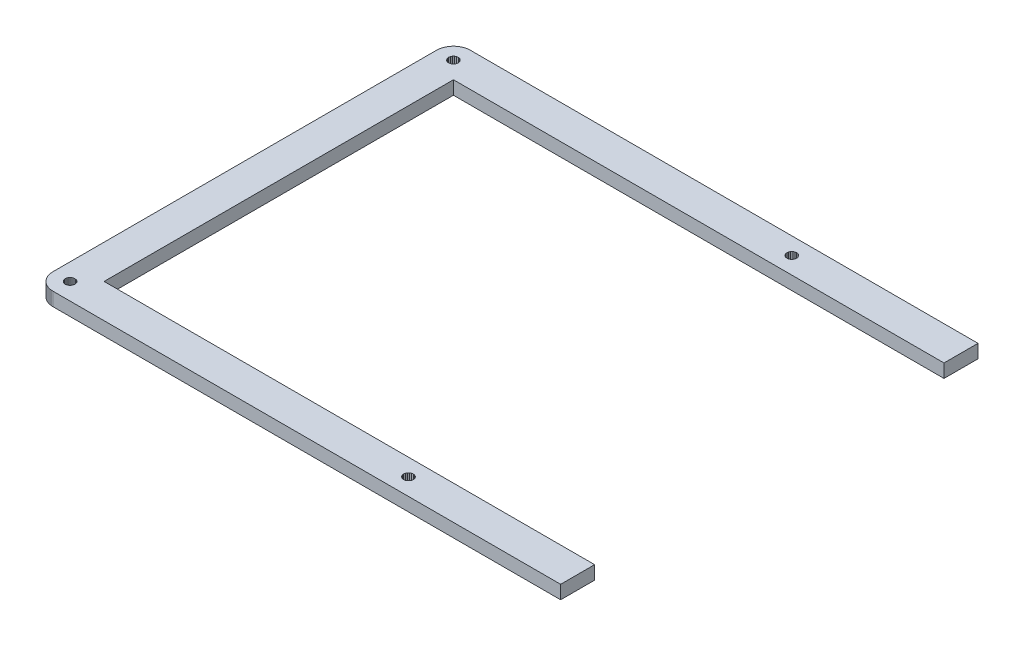
SolidWorks part; units mm, degrees
material "Copper"
ref_plane "Front Plane" through (0, 0, 0) normal (0, 0, 1) x (1, 0, 0)
ref_plane "Top Plane" through (0, 0, 0) normal (0, 1, 0) x (1, 0, 0)
ref_plane "Right Plane" through (0, 0, 0) normal (1, 0, 0) x (0, 0, -1)
sketch "Sketch1" plane through (0, 0, 0) normal (0, 1, 0) x (1, 0, 0)
  line L0 (365.806, 147.967) -> (366.279, 147.949)
  line L1 (366.279, 147.949) -> (366.748, 147.894)
  line L2 (366.748, 147.894) -> (367.21, 147.803)
  line L3 (367.21, 147.803) -> (367.661, 147.675)
  line L4 (367.661, 147.675) -> (368.106, 147.511)
  line L5 (368.106, 147.511) -> (368.533, 147.314)
  line L6 (368.533, 147.314) -> (368.942, 147.085)
  line L7 (368.942, 147.085) -> (369.334, 146.822)
  line L8 (369.334, 146.822) -> (369.704, 146.529)
  line L9 (369.704, 146.529) -> (370.05, 146.21)
  line L10 (370.05, 146.21) -> (370.371, 145.865)
  line L11 (370.371, 145.865) -> (370.664, 145.495)
  line L12 (370.664, 145.495) -> (370.925, 145.102)
  line L13 (370.925, 145.102) -> (371.154, 144.691)
  line L14 (371.154, 144.691) -> (371.352, 144.264)
  line L15 (371.352, 144.264) -> (371.514, 143.822)
  line L16 (371.514, 143.822) -> (371.641, 143.368)
  line L17 (371.641, 143.368) -> (371.733, 142.907)
  line L18 (371.733, 142.907) -> (371.789, 142.44)
  line L19 (371.789, 142.44) -> (371.807, 141.967)
  line L20 (371.807, 141.967) -> (371.807, 6.0909)
  line L21 (371.807, 6.0909) -> (371.789, 5.621)
  line L22 (371.789, 5.621) -> (371.733, 5.1539)
  line L23 (371.733, 5.1539) -> (371.641, 4.6909)
  line L24 (371.641, 4.6909) -> (371.514, 4.2375)
  line L25 (371.514, 4.2375) -> (371.352, 3.7951)
  line L26 (371.352, 3.7951) -> (371.154, 3.3679)
  line L27 (371.154, 3.3679) -> (370.925, 2.9573)
  line L28 (370.925, 2.9573) -> (370.664, 2.5645)
  line L29 (370.664, 2.5645) -> (370.371, 2.1966)
  line L30 (370.371, 2.1966) -> (370.05, 1.8493)
  line L31 (370.05, 1.8493) -> (369.704, 1.5296)
  line L32 (369.704, 1.5296) -> (369.334, 1.2375)
  line L33 (369.334, 1.2375) -> (368.942, 0.9757)
  line L34 (368.942, 0.9757) -> (368.533, 0.7455)
  line L35 (368.533, 0.7455) -> (368.106, 0.5498)
  line L36 (368.106, 0.5498) -> (367.661, 0.3859)
  line L37 (367.661, 0.3859) -> (367.21, 0.2577)
  line L38 (367.21, 0.2577) -> (366.748, 0.1654)
  line L39 (366.748, 0.1654) -> (366.279, 0.1102)
  line L40 (366.279, 0.1102) -> (365.806, 0.091)
  line L41 (365.806, 0.091) -> (6.095, 0.091)
  line L42 (6.095, 0.091) -> (5.6238, 0.1102)
  line L43 (5.6238, 0.1102) -> (5.1553, 0.1654)
  line L44 (5.1553, 0.1654) -> (4.6936, 0.2577)
  line L45 (4.6936, 0.2577) -> (4.2402, 0.3859)
  line L46 (4.2402, 0.3859) -> (3.7979, 0.5498)
  line L47 (3.7979, 0.5498) -> (3.3707, 0.7455)
  line L48 (3.3707, 0.7455) -> (2.96, 0.9757)
  line L49 (2.96, 0.9757) -> (2.5673, 1.2375)
  line L50 (2.5673, 1.2375) -> (2.198, 1.5296)
  line L51 (2.198, 1.5296) -> (1.8521, 1.8493)
  line L52 (1.8521, 1.8493) -> (1.5324, 2.1966)
  line L53 (1.5324, 2.1966) -> (1.2402, 2.5645)
  line L54 (1.2402, 2.5645) -> (0.9784, 2.9573)
  line L55 (0.9784, 2.9573) -> (0.7483, 3.3679)
  line L56 (0.7483, 3.3679) -> (0.5512, 3.7951)
  line L57 (0.5512, 3.7951) -> (0.3872, 4.2375)
  line L58 (0.3872, 4.2375) -> (0.2591, 4.6909)
  line L59 (0.2591, 4.6909) -> (0.1681, 5.1539)
  line L60 (0.1681, 5.1539) -> (0.113, 5.621)
  line L61 (0.113, 5.621) -> (0.0937, 6.0923)
  line L62 (0.0937, 6.0923) -> (0.0951, 141.967)
  line L63 (0.0951, 141.967) -> (0.113, 142.44)
  line L64 (0.113, 142.44) -> (0.1681, 142.907)
  line L65 (0.1681, 142.907) -> (0.2591, 143.368)
  line L66 (0.2591, 143.368) -> (0.3872, 143.822)
  line L67 (0.3872, 143.822) -> (0.5512, 144.264)
  line L68 (0.5512, 144.264) -> (0.7483, 144.691)
  line L69 (0.7483, 144.691) -> (0.9784, 145.102)
  line L70 (0.9784, 145.102) -> (1.2402, 145.495)
  line L71 (1.2402, 145.495) -> (1.5324, 145.865)
  line L72 (1.5324, 145.865) -> (1.8521, 146.21)
  line L73 (1.8521, 146.21) -> (2.198, 146.529)
  line L74 (2.198, 146.529) -> (2.5673, 146.822)
  line L75 (2.5673, 146.822) -> (2.96, 147.085)
  line L76 (2.96, 147.085) -> (3.3707, 147.314)
  line L77 (3.3707, 147.314) -> (3.7979, 147.511)
  line L78 (3.7979, 147.511) -> (4.2402, 147.675)
  line L79 (4.2402, 147.675) -> (4.6936, 147.803)
  line L80 (4.6936, 147.803) -> (5.1553, 147.894)
  line L81 (5.1553, 147.894) -> (5.6238, 147.949)
  line L82 (5.6238, 147.949) -> (6.095, 147.968)
  line L83 (6.095, 147.968) -> (365.806, 147.967)
  line L84 (365.252, 7.757) -> (364.769, 7.5117)
  line L85 (364.769, 7.5117) -> (364.388, 7.13)
  line L86 (364.388, 7.13) -> (364.141, 6.6504)
  line L87 (364.141, 6.6504) -> (364.06, 6.1157)
  line L88 (364.06, 6.1157) -> (364.141, 5.5838)
  line L89 (364.141, 5.5838) -> (364.388, 5.1029)
  line L90 (364.388, 5.1029) -> (364.769, 4.7211)
  line L91 (364.769, 4.7211) -> (365.252, 4.4759)
  line L92 (365.252, 4.4759) -> (365.781, 4.3918)
  line L93 (365.781, 4.3918) -> (366.317, 4.4759)
  line L94 (366.317, 4.4759) -> (366.797, 4.7211)
  line L95 (366.797, 4.7211) -> (367.178, 5.1029)
  line L96 (367.178, 5.1029) -> (367.425, 5.5838)
  line L97 (367.425, 5.5838) -> (367.506, 6.1157)
  line L98 (367.506, 6.1157) -> (367.425, 6.6504)
  line L99 (367.425, 6.6504) -> (367.178, 7.13)
  line L100 (367.178, 7.13) -> (366.797, 7.5117)
  line L101 (366.797, 7.5117) -> (366.317, 7.757)
  line L102 (366.317, 7.757) -> (365.781, 7.8411)
  line L103 (365.781, 7.8411) -> (365.252, 7.757)
  line L104 (245.361, 7.757) -> (244.88, 7.5117)
  line L105 (244.88, 7.5117) -> (244.5, 7.13)
  line L106 (244.5, 7.13) -> (244.255, 6.6504)
  line L107 (244.255, 6.6504) -> (244.169, 6.1157)
  line L108 (244.169, 6.1157) -> (244.255, 5.5838)
  line L109 (244.255, 5.5838) -> (244.5, 5.1029)
  line L110 (244.5, 5.1029) -> (244.88, 4.7211)
  line L111 (244.88, 4.7211) -> (245.361, 4.4759)
  line L112 (245.361, 4.4759) -> (245.894, 4.3918)
  line L113 (245.894, 4.3918) -> (246.428, 4.4759)
  line L114 (246.428, 4.4759) -> (246.908, 4.7211)
  line L115 (246.908, 4.7211) -> (247.29, 5.1029)
  line L116 (247.29, 5.1029) -> (247.536, 5.5838)
  line L117 (247.536, 5.5838) -> (247.62, 6.1157)
  line L118 (247.62, 6.1157) -> (247.536, 6.6504)
  line L119 (247.536, 6.6504) -> (247.29, 7.13)
  line L120 (247.29, 7.13) -> (246.908, 7.5117)
  line L121 (246.908, 7.5117) -> (246.428, 7.757)
  line L122 (246.428, 7.757) -> (245.894, 7.8411)
  line L123 (245.894, 7.8411) -> (245.361, 7.757)
  line L124 (125.473, 7.757) -> (124.992, 7.5117)
  line L125 (124.992, 7.5117) -> (124.612, 7.13)
  line L126 (124.612, 7.13) -> (124.365, 6.6504)
  line L127 (124.365, 6.6504) -> (124.281, 6.1157)
  line L128 (124.281, 6.1157) -> (124.365, 5.5838)
  line L129 (124.365, 5.5838) -> (124.612, 5.1029)
  line L130 (124.612, 5.1029) -> (124.992, 4.7211)
  line L131 (124.992, 4.7211) -> (125.473, 4.4759)
  line L132 (125.473, 4.4759) -> (126.007, 4.3918)
  line L133 (126.007, 4.3918) -> (126.54, 4.4759)
  line L134 (126.54, 4.4759) -> (127.021, 4.7211)
  line L135 (127.021, 4.7211) -> (127.403, 5.1029)
  line L136 (127.403, 5.1029) -> (127.648, 5.5838)
  line L137 (127.648, 5.5838) -> (127.732, 6.1157)
  line L138 (127.732, 6.1157) -> (127.648, 6.6504)
  line L139 (127.648, 6.6504) -> (127.403, 7.13)
  line L140 (127.403, 7.13) -> (127.021, 7.5117)
  line L141 (127.021, 7.5117) -> (126.54, 7.757)
  line L142 (126.54, 7.757) -> (126.007, 7.8411)
  line L143 (126.007, 7.8411) -> (125.473, 7.757)
  line L144 (5.5852, 7.757) -> (5.1056, 7.5117)
  line L145 (5.1056, 7.5117) -> (4.7239, 7.13)
  line L146 (4.7239, 7.13) -> (4.4786, 6.6504)
  line L147 (4.4786, 6.6504) -> (4.3932, 6.1157)
  line L148 (4.3932, 6.1157) -> (4.4786, 5.5838)
  line L149 (4.4786, 5.5838) -> (4.7239, 5.1029)
  line L150 (4.7239, 5.1029) -> (5.1056, 4.7211)
  line L151 (5.1056, 4.7211) -> (5.5852, 4.4759)
  line L152 (5.5852, 4.4759) -> (6.1185, 4.3918)
  line L153 (6.1185, 4.3918) -> (6.6532, 4.4759)
  line L154 (6.6532, 4.4759) -> (7.1327, 4.7211)
  line L155 (7.1327, 4.7211) -> (7.5145, 5.1029)
  line L156 (7.5145, 5.1029) -> (7.7597, 5.5838)
  line L157 (7.7597, 5.5838) -> (7.8438, 6.1157)
  line L158 (7.8438, 6.1157) -> (7.7597, 6.6504)
  line L159 (7.7597, 6.6504) -> (7.5145, 7.13)
  line L160 (7.5145, 7.13) -> (7.1327, 7.5117)
  line L161 (7.1327, 7.5117) -> (6.6532, 7.757)
  line L162 (6.6532, 7.757) -> (6.1185, 7.8411)
  line L163 (6.1185, 7.8411) -> (5.5852, 7.757)
  line L164 (12.1447, 135.919) -> (359.759, 135.919)
  line L165 (359.759, 135.919) -> (359.759, 12.1405)
  line L166 (359.759, 12.1405) -> (12.1447, 12.1405)
  line L167 (12.1447, 12.1405) -> (12.1447, 135.919)
  line L168 (125.473, 143.583) -> (124.992, 143.338)
  line L169 (124.992, 143.338) -> (124.612, 142.956)
  line L170 (124.612, 142.956) -> (124.365, 142.477)
  line L171 (124.365, 142.477) -> (124.281, 141.942)
  line L172 (124.281, 141.942) -> (124.365, 141.409)
  line L173 (124.365, 141.409) -> (124.612, 140.929)
  line L174 (124.612, 140.929) -> (124.992, 140.547)
  line L175 (124.992, 140.547) -> (125.473, 140.302)
  line L176 (125.473, 140.302) -> (126.007, 140.217)
  line L177 (126.007, 140.217) -> (126.54, 140.302)
  line L178 (126.54, 140.302) -> (127.021, 140.547)
  line L179 (127.021, 140.547) -> (127.403, 140.929)
  line L180 (127.403, 140.929) -> (127.648, 141.409)
  line L181 (127.648, 141.409) -> (127.732, 141.942)
  line L182 (127.732, 141.942) -> (127.648, 142.477)
  line L183 (127.648, 142.477) -> (127.403, 142.956)
  line L184 (127.403, 142.956) -> (127.021, 143.338)
  line L185 (127.021, 143.338) -> (126.54, 143.583)
  line L186 (126.54, 143.583) -> (126.007, 143.667)
  line L187 (126.007, 143.667) -> (125.473, 143.583)
  line L188 (245.361, 143.583) -> (244.88, 143.338)
  line L189 (244.88, 143.338) -> (244.5, 142.956)
  line L190 (244.5, 142.956) -> (244.255, 142.477)
  line L191 (244.255, 142.477) -> (244.169, 141.942)
  line L192 (244.169, 141.942) -> (244.255, 141.409)
  line L193 (244.255, 141.409) -> (244.5, 140.929)
  line L194 (244.5, 140.929) -> (244.88, 140.547)
  line L195 (244.88, 140.547) -> (245.361, 140.302)
  line L196 (245.361, 140.302) -> (245.894, 140.217)
  line L197 (245.894, 140.217) -> (246.428, 140.302)
  line L198 (246.428, 140.302) -> (246.908, 140.547)
  line L199 (246.908, 140.547) -> (247.29, 140.929)
  line L200 (247.29, 140.929) -> (247.536, 141.409)
  line L201 (247.536, 141.409) -> (247.62, 141.942)
  line L202 (247.62, 141.942) -> (247.536, 142.477)
  line L203 (247.536, 142.477) -> (247.29, 142.956)
  line L204 (247.29, 142.956) -> (246.908, 143.338)
  line L205 (246.908, 143.338) -> (246.428, 143.583)
  line L206 (246.428, 143.583) -> (245.894, 143.667)
  line L207 (245.894, 143.667) -> (245.361, 143.583)
  line L208 (365.252, 143.583) -> (364.769, 143.338)
  line L209 (364.769, 143.338) -> (364.388, 142.956)
  line L210 (364.388, 142.956) -> (364.141, 142.477)
  line L211 (364.141, 142.477) -> (364.06, 141.942)
  line L212 (364.06, 141.942) -> (364.141, 141.409)
  line L213 (364.141, 141.409) -> (364.388, 140.929)
  line L214 (364.388, 140.929) -> (364.769, 140.547)
  line L215 (364.769, 140.547) -> (365.252, 140.302)
  line L216 (365.252, 140.302) -> (365.781, 140.217)
  line L217 (365.781, 140.217) -> (366.317, 140.302)
  line L218 (366.317, 140.302) -> (366.797, 140.547)
  line L219 (366.797, 140.547) -> (367.178, 140.929)
  line L220 (367.178, 140.929) -> (367.425, 141.409)
  line L221 (367.425, 141.409) -> (367.506, 141.942)
  line L222 (367.506, 141.942) -> (367.425, 142.477)
  line L223 (367.425, 142.477) -> (367.178, 142.956)
  line L224 (367.178, 142.956) -> (366.797, 143.338)
  line L225 (366.797, 143.338) -> (366.317, 143.583)
  line L226 (366.317, 143.583) -> (365.781, 143.667)
  line L227 (365.781, 143.667) -> (365.252, 143.583)
  line L228 (5.5852, 143.583) -> (5.1056, 143.338)
  line L229 (5.1056, 143.338) -> (4.7239, 142.956)
  line L230 (4.7239, 142.956) -> (4.4786, 142.477)
  line L231 (4.4786, 142.477) -> (4.3932, 141.942)
  line L232 (4.3932, 141.942) -> (4.4786, 141.409)
  line L233 (4.4786, 141.409) -> (4.7239, 140.929)
  line L234 (4.7239, 140.929) -> (5.1056, 140.547)
  line L235 (5.1056, 140.547) -> (5.5852, 140.302)
  line L236 (5.5852, 140.302) -> (6.1185, 140.217)
  line L237 (6.1185, 140.217) -> (6.6532, 140.302)
  line L238 (6.6532, 140.302) -> (7.1327, 140.547)
  line L239 (7.1327, 140.547) -> (7.5145, 140.929)
  line L240 (7.5145, 140.929) -> (7.7597, 141.409)
  line L241 (7.7597, 141.409) -> (7.8438, 141.942)
  line L242 (7.8438, 141.942) -> (7.7597, 142.477)
  line L243 (7.7597, 142.477) -> (7.5145, 142.956)
  line L244 (7.5145, 142.956) -> (7.1327, 143.338)
  line L245 (7.1327, 143.338) -> (6.6532, 143.583)
  line L246 (6.6532, 143.583) -> (6.1185, 143.667)
  line L247 (6.1185, 143.667) -> (5.5852, 143.583)
  line L248 (185.9505, 147.9675) -> (185.9505, 0.091)
extrude "Boss-Extrude2" add sketch "Sketch1" along normal blind 4.7625 contours L248 L83 L82 L81 L80 L79 L78 L77 L76 L75 L74 L73 L72 L71 L70 L69 L68 L67 L66 L65 L64 L63 L62 L61 L60 L59 L58 L57 L56 L55 L54 L53 L52 L51 L50 L49 L48 L47 L46 L45 L44 L43 L42 L41 L166 L167 L164 L247 L246
